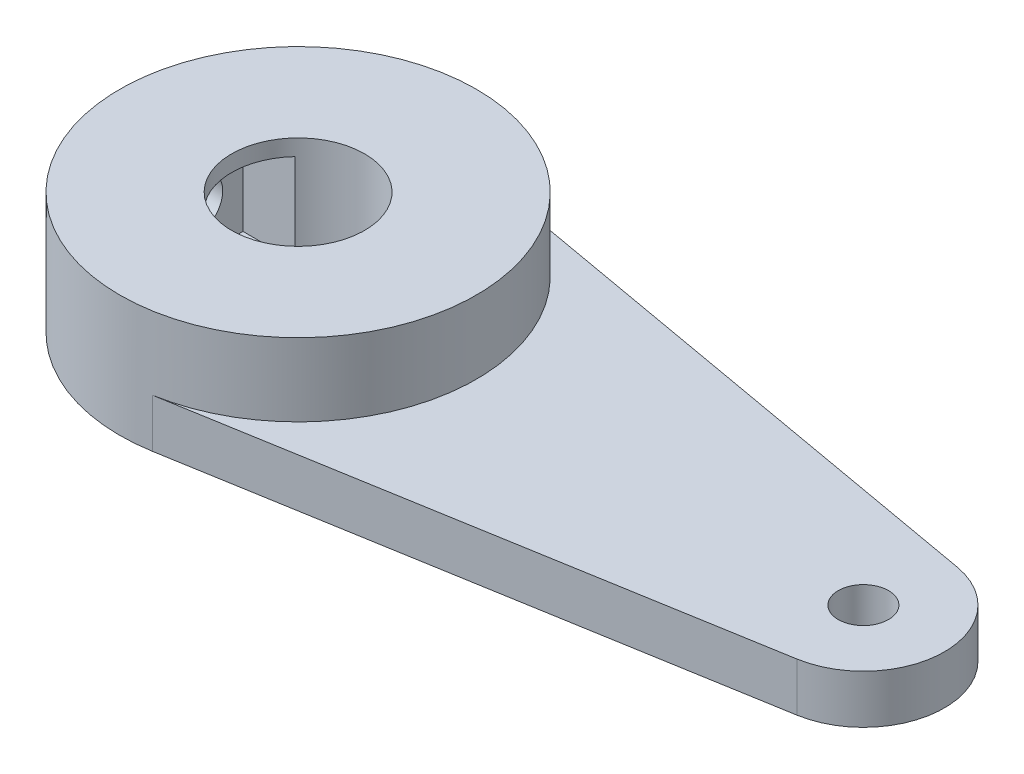
SolidWorks part; units mm, degrees
ref_plane "前视基准面" through (0, 0, 0) normal (0, 0, 1) x (1, 0, 0)
ref_plane "上视基准面" through (0, 0, 0) normal (0, 1, 0) x (1, 0, 0)
ref_plane "右视基准面" through (0, 0, 0) normal (1, 0, 0) x (0, 0, -1)
sketch "草图2" plane through (0, 0, 0) normal (0, 1, 0) x (1, 0, 0)
  line L0 (1.9246, 10.8303) -> (35.8748, 4.7973)
  line L1 (35.8395, -5.0546) -> (1.8468, -10.8439)
  arc A0 (1.9246, 10.8303) -> (1.8468, -10.8439) centre (0, 0) ccw
  arc A1 (35.8748, 4.7973) -> (35.8395, -5.0546) centre (35, -0.1255) cw
  dimension "D1" = 22
  dimension "D3" = 5
  dimension "D2" = 35
extrude "凸台-拉伸1" add sketch "草图2" along normal blind 3
sketch "草图4" plane through (0, 3, 0) normal (0, 1, 0) x (1, 0, 0)
  circle A0 centre (0, 0) radius 11
  dimension "D1" = 22
extrude "凸台-拉伸2" add sketch "草图4" along normal blind 4.5
sketch "草图5" plane through (0, 0, 0) normal (0, -1, 0) x (1, 0, 0)
  circle A0 centre (0, 0) radius 4.1
  circle A1 centre (35, 0.1255) radius 1.55
  dimension "D1" = 8.2
  dimension "D2" = 3.1
extrude "切除-拉伸1" cut sketch "草图5" against normal through all
ref_plane "基准面1" through (-4.1, 0, 0) normal (1, 0, 0) x (0, 0, -1)
sketch "草图7" plane through (-4.1, 0, 0) normal (1, 0, 0) x (0, 0, -1)
  line L0 (0, 0) -> (0, 3.7) construction
  line L1 (-2.8, 6.5) -> (2.8, 6.5)
  line L2 (-2.8, 6.5) -> (-2.8, 0.9)
  line L3 (-2.8, 0.9) -> (2.8, 0.9)
  line L4 (2.8, 6.5) -> (2.8, 0.9)
  line L5 (-2.8, 6.5) -> (2.8, 0.9) construction
  line L6 (-2.8, 0.9) -> (2.8, 6.5) construction
  line L7 (-5.0546, 0) -> (4.7973, 0) construction
  point P0 (0, 3.7)
  dimension "D1" = 5.6
  dimension "D2" = 5.6
  dimension "D3" = 3.7
extrude "切除-四方薄螺母" cut sketch "草图7" against normal mid plane 4.2
sketch "草图8" plane through (-4.1, 0, 0) normal (1, 0, 0) x (0, 0, -1)
  line L0 (0, 0) -> (0, 10.8987) construction
  line L1 (-5.0546, 0) -> (4.7973, 0) construction
  circle A0 centre (0, 3.7) radius 1.55
  dimension "D1" = 3.1
  dimension "D2" = 3.7
extrude "切除-M3孔" cut sketch "草图8" against normal through all
